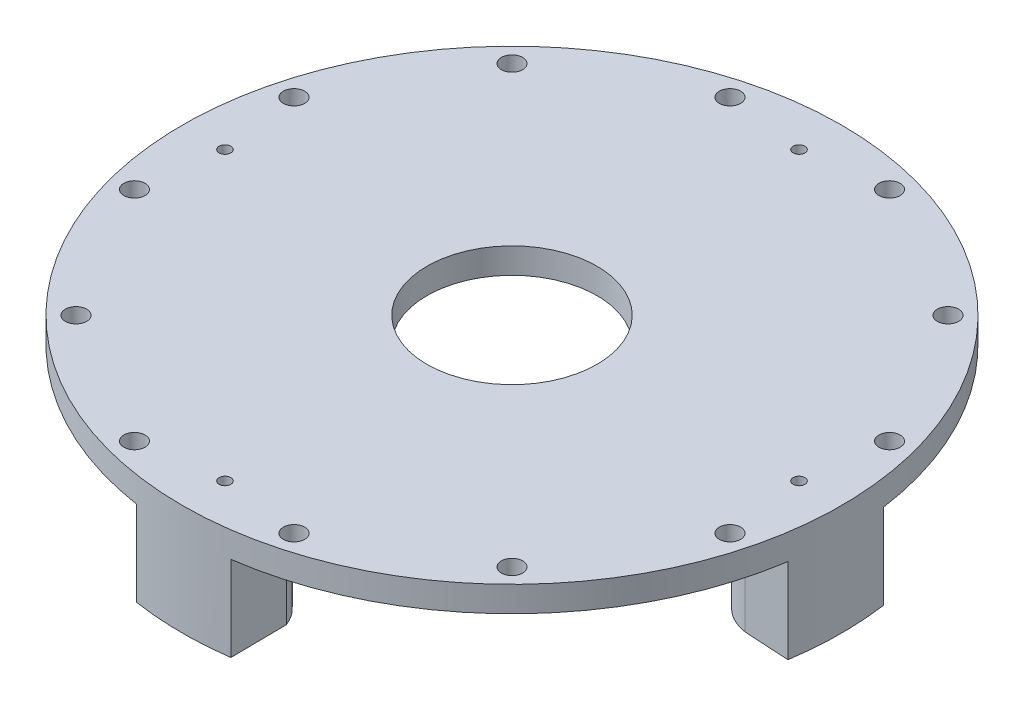
SolidWorks part; units mm, degrees
material "6061-T6 (SS)"
ref_plane "Front Plane" through (0, 0, 0) normal (0, 0, 1) x (1, 0, 0)
ref_plane "Top Plane" through (0, 0, 0) normal (0, 1, 0) x (1, 0, 0)
ref_plane "Right Plane" through (0, 0, 0) normal (1, 0, 0) x (0, 0, -1)
sketch "Sketch1" plane through (0, 0, 0) normal (0, 1, 0) x (1, 0, 0)
  circle A0 centre (0, 0) radius 98.425
  circle A1 centre (0, 0) radius 25.4
  dimension "D1" = 196.85
  dimension "D2" = 50.8
extrude "Boss-Extrude1" add sketch "Sketch1" along normal blind 7.62
sketch "Sketch2" plane through (0, 0, 0) normal (0, -1, 0) x (1, 0, 0)
  line L0 (0, 0) -> (0, 75.6548) construction
  line L1 (13.05, 85.725) -> (0.0025, 85.725) construction
  line L2 (-12.7, 85.725) -> (-1009.5225, 85.725) construction
  line L3 (0, 73.025) -> (0, 50000) construction
  line L4 (-14.0929, 83.7516) -> (-14.8752, 97.2945)
  line L6 (13.5312, 97.4904) -> (13.3337, 80.7532)
  line L13 (83.7516, 14.0929) -> (97.2945, 14.8752)
  line L14 (97.4904, -13.5312) -> (80.7532, -13.3337)
  line L15 (14.0929, -83.7516) -> (14.8752, -97.2945)
  line L16 (-13.5312, -97.4904) -> (-13.3337, -80.7532)
  line L17 (-83.7516, -14.0929) -> (-97.2945, -14.8752)
  line L18 (-97.4904, 13.5312) -> (-80.7532, 13.3337)
  arc A0 (0.1408, 73.0258) -> (0, 73.025) centre (0, 85.725) ccw construction
  circle A1 centre (0, 0) radius 98.425 construction
  arc A10 (-14.0929, 83.7516) -> (13.3337, 80.7532) centre (0, 85.725) ccw
  arc A25 (-14.8752, 97.2945) -> (13.5312, 97.4904) centre (0, 0) cw
  arc A26 (97.2945, 14.8752) -> (97.4904, -13.5312) centre (0, 0) cw
  arc A27 (83.7516, 14.0929) -> (80.7532, -13.3337) centre (85.725, 0) ccw
  arc A28 (14.8752, -97.2945) -> (-13.5312, -97.4904) centre (0, 0) cw
  arc A29 (14.0929, -83.7516) -> (-13.3337, -80.7532) centre (0, -85.725) ccw
  arc A30 (-97.2945, -14.8752) -> (-97.4904, 13.5312) centre (0, 0) cw
  arc A31 (-83.7516, -14.0929) -> (-80.7532, 13.3337) centre (-85.725, 0) ccw
  point P7 (-12.7, 85.725)
  point P8 (12.7, 85.725)
  point P9 (12.2673, 82.438)
  point P13 (0, 93.5788)
  point P17 (-12.2673, 82.438)
  point P26 (12.556, 85.725)
  point P27 (-12.6299, 85.725)
  point P28 (-12.6299, 85.725)
  point P44 (0, 0)
  point P52 (0, 0)
  dimension "D1" = 4
  dimension "D2" = 85.725
extrude "Boss-Extrude2" add sketch "Sketch2" along normal blind 25.4
sketch "Sketch4" plane through (0, 7.62, 0) normal (0, 1, 0) x (1, 0, 0)
  line L0 (0, 0) -> (23.8636, 89.0603) construction
  line L1 (0, 0) -> (0, 98.425) construction
  circle A0 centre (23.8636, 89.0603) radius 3.175
  circle A1 centre (65.1967, 65.1967) radius 3.175
  circle A2 centre (89.0603, 23.8636) radius 3.175
  circle A3 centre (89.0603, -23.8636) radius 3.175
  circle A4 centre (65.1967, -65.1967) radius 3.175
  circle A5 centre (23.8636, -89.0603) radius 3.175
  circle A6 centre (-23.8636, -89.0603) radius 3.175
  circle A7 centre (-65.1967, -65.1967) radius 3.175
  circle A8 centre (-89.0603, -23.8636) radius 3.175
  circle A9 centre (-89.0603, 23.8636) radius 3.175
  circle A10 centre (-65.1967, 65.1967) radius 3.175
  circle A11 centre (-23.8636, 89.0603) radius 3.175
  circle A12 centre (0, 0) radius 98.425 construction
  point P28 (0, 0)
  dimension "D1" = 6.35
  dimension "D3" = 12
  dimension "D2" = 92.202
  dimension "D4" = 15
sketch "Sketch5" plane through (0, -25.4, 0) normal (0, -1, 0) x (1, 0, 0)
  line L0 (200013.05, 85.725) -> (-199999.9975, 85.725) construction
  line L1 (0, 73.025) -> (0, 250000) construction
  line L2 (200013.05, 85.725) -> (-199999.9975, 85.725) construction
  line L3 (0, 73.025) -> (0, 250000) construction
  circle A0 centre (0, 85.725) radius 5.2578
  point P17 (0.7848, -0.7848)
  dimension "D1" = 10.5156
  dimension "D2" = 85.725
extrude "Cut-Extrude3" cut sketch "Sketch5" against normal blind 19.05
sketch "Sketch6" plane through (0, 7.62, 0) normal (0, 1, 0) x (1, 0, 0)
  line L0 (0, 0) -> (0, 98.425) construction
  line L1 (0, 0) -> (-25.4743, 95.0712) construction
  circle A0 centre (0, 0) radius 98.425 construction
  circle A1 centre (-23.8308, 88.9376) radius 3.175
  point P33 (0, 0)
  dimension "D2" = 6.35
  dimension "D1" = 15
  dimension "D3" = 92.075
extrude "Cut-Extrude4" cut sketch "Sketch6" against normal blind 12.7
extrude "Cut-Extrude2" [suppressed] cut sketch "Sketch4" against normal blind 12.7
pattern_circular "CirPattern1" count 12 over 360 about axis through (0, 0, 0) along (0, 1, 0) of "Cut-Extrude4"
pattern_circular "CirPattern2" count 4 over 360 about axis through (0, 0, 0) along (0, 1, 0) of "Cut-Extrude3"
ref_plane "Plane1" through (0, 7.62, 0) normal (0, 1, 0) x (1, 0, 0)
sketch "Sketch8" plane through (0, 7.62, 0) normal (0, 1, 0) x (1, 0, 0)
  circle A0 centre (0, 85.725) radius 1.7526
  dimension "D1" = 3.5052
extrude "Cut-Extrude6" cut sketch "Sketch8" against normal through all
pattern_circular "CirPattern3" count 4 over 360 about axis through (0, 0, 0) along (0, 1, 0) of "Cut-Extrude6"
sketch "Sketch9" plane through (0, 7.62, 0) normal (0, 1, 0) x (1, 0, 0)
  circle A0 centre (0, 0) radius 98.425 construction
  point P0 (0, 85.725)
  point P1 (0, 98.425)
